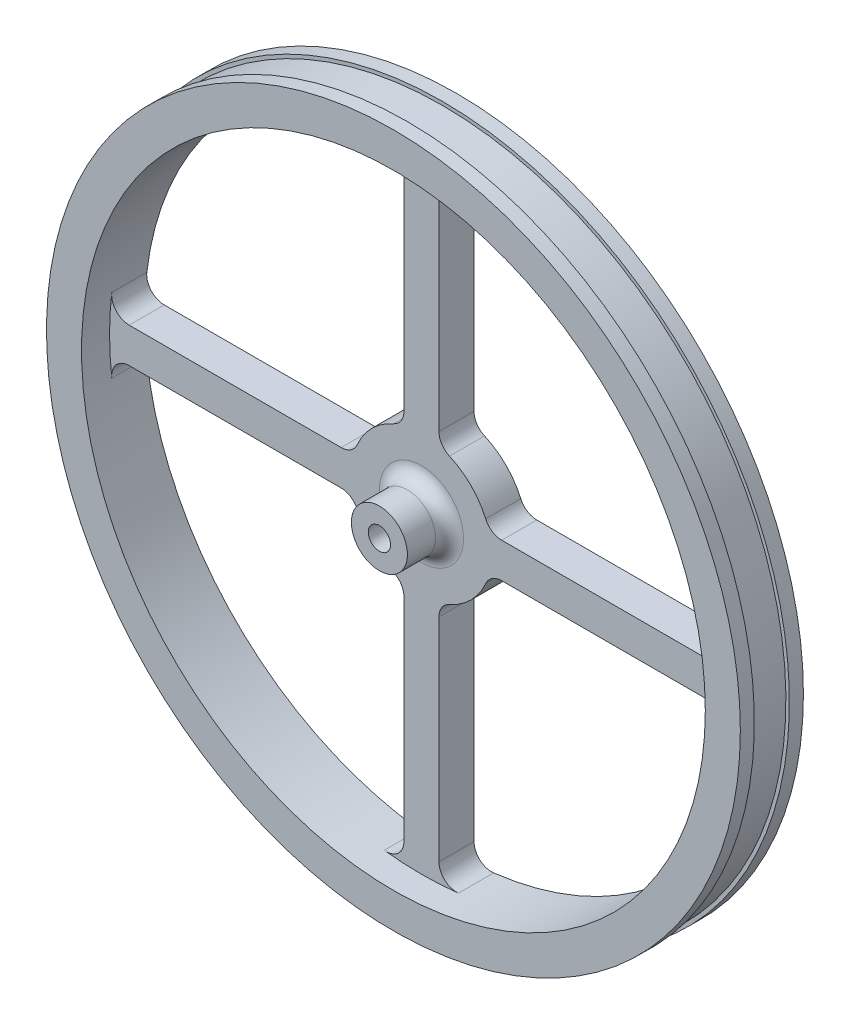
SolidWorks part; units mm, degrees
ref_plane "Front Plane" through (0, 0, 0) normal (0, 0, 1) x (1, 0, 0)
ref_plane "Top Plane" through (0, 0, 0) normal (0, 1, 0) x (1, 0, 0)
ref_plane "Right Plane" through (0, 0, 0) normal (1, 0, 0) x (0, 0, -1)
sketch "Sketch1" plane through (0, 0, 0) normal (0, 0, 1) x (1, 0, 0)
  circle A0 centre (0, 0) radius 49.5
  circle A1 centre (0, 0) radius 1.5875
  dimension "D1" = 99
  dimension "D2" = 3.175
extrude "Boss-Extrude1" add sketch "Sketch1" along normal blind 9
sketch "Sketch2" plane through (0, 0, 9) normal (0, 0, 1) x (1, 0, 0)
  line L8 (0, 7.5) -> (0, 47) construction
  line L9 (7.5, 0) -> (47, 0) construction
  line L10 (2.5, 11.4564) -> (2.5, 41.7013)
  line L11 (11.4564, 2.5) -> (41.7013, 2.5)
  line L12 (9.6825, 2.5) -> (44.4297, 2.5) construction
  line L13 (2.5, 9.6825) -> (2.5, 44.4297) construction
  line L18 (-11.4564, 2.5) -> (-41.7013, 2.5)
  line L19 (-2.5, 11.4564) -> (-2.5, 41.7013)
  line L22 (-7.5, 0) -> (-47, 0) construction
  line L23 (0, 7.5) -> (0, 47) construction
  line L32 (-2.5, -11.4564) -> (-2.5, -41.7013)
  line L33 (-11.4564, -2.5) -> (-41.7013, -2.5)
  line L36 (0, -7.5) -> (0, -47) construction
  line L37 (-7.5, 0) -> (-47, 0) construction
  line L40 (11.4564, -2.5) -> (41.7013, -2.5)
  line L41 (2.5, -11.4564) -> (2.5, -41.7013)
  line L44 (7.5, 0) -> (47, 0) construction
  line L45 (0, -7.5) -> (0, -47) construction
  line L58 (0, 0) -> (0, -14.5334) [skipped]
  line L59 (0, 0) -> (-57.9228, 0) [skipped]
  circle A1 centre (0, 0) radius 49.5 construction
  arc A33 (7.5, 0) -> (0, 7.5) centre (0, 0) ccw construction
  arc A36 (47, 0) -> (0, 47) centre (0, 0) ccw construction
  arc A46 (44.1835, 5.2976) -> (5.2976, 44.1835) centre (0, 0) ccw
  arc A53 (9.1652, 4) -> (4, 9.1652) centre (0, 0) ccw
  arc A54 (44.4297, 2.5) -> (2.5, 44.4297) centre (0, 0) ccw construction
  arc A61 (44.1835, 5.2976) -> (41.7013, 2.5) centre (41.7013, 5) cw
  arc A62 (9.6825, 2.5) -> (2.5, 9.6825) centre (0, 0) ccw construction
  arc A69 (11.4564, 2.5) -> (9.1652, 4) centre (11.4564, 5) cw
  arc A70 (2.5, 11.4564) -> (4, 9.1652) centre (5, 11.4564) ccw
  arc A77 (2.5, 41.7013) -> (5.2976, 44.1835) centre (5, 41.7013) cw
  arc A78 (-5.2976, 44.1835) -> (-44.1835, 5.2976) centre (0, 0) ccw
  arc A85 (-4, 9.1652) -> (-9.1652, 4) centre (0, 0) ccw
  arc A86 (-5.2976, 44.1835) -> (-2.5, 41.7013) centre (-5, 41.7013) cw
  arc A93 (-2.5, 11.4564) -> (-4, 9.1652) centre (-5, 11.4564) cw
  arc A94 (-11.4564, 2.5) -> (-9.1652, 4) centre (-11.4564, 5) ccw
  arc A96 (-41.7013, 2.5) -> (-44.1835, 5.2976) centre (-41.7013, 5) cw
  arc A97 (0, 7.5) -> (-7.5, 0) centre (0, 0) ccw construction
  arc A98 (0, 47) -> (-47, 0) centre (0, 0) ccw construction
  arc A99 (-44.1835, -5.2976) -> (-5.2976, -44.1835) centre (0, 0) ccw
  arc A100 (-9.1652, -4) -> (-4, -9.1652) centre (0, 0) ccw
  arc A101 (-44.1835, -5.2976) -> (-41.7013, -2.5) centre (-41.7013, -5) cw
  arc A102 (-11.4564, -2.5) -> (-9.1652, -4) centre (-11.4564, -5) cw
  arc A103 (-2.5, -11.4564) -> (-4, -9.1652) centre (-5, -11.4564) ccw
  arc A104 (-2.5, -41.7013) -> (-5.2976, -44.1835) centre (-5, -41.7013) cw
  arc A105 (-7.5, 0) -> (0, -7.5) centre (0, 0) ccw construction
  arc A106 (-47, 0) -> (0, -47) centre (0, 0) ccw construction
  arc A107 (5.2976, -44.1835) -> (44.1835, -5.2976) centre (0, 0) ccw
  arc A108 (4, -9.1652) -> (9.1652, -4) centre (0, 0) ccw
  arc A109 (5.2976, -44.1835) -> (2.5, -41.7013) centre (5, -41.7013) cw
  arc A110 (2.5, -11.4564) -> (4, -9.1652) centre (5, -11.4564) cw
  arc A111 (11.4564, -2.5) -> (9.1652, -4) centre (11.4564, -5) ccw
  arc A112 (41.7013, -2.5) -> (44.1835, -5.2976) centre (41.7013, -5) cw
  arc A113 (0, -7.5) -> (7.5, 0) centre (0, 0) ccw construction
  arc A114 (0, -47) -> (47, 0) centre (0, 0) ccw construction
  point P15 (0, 0)
  point P41 (0, 0)
  point P58 (0, 0)
  point P86 (0, 0)
  point P99 (0, 0)
  dimension "D1" = 4
  dimension "D2" = 2.5
  dimension "D4" = 5
  dimension "D3" = 2.5
  dimension "D5" = 10
extrude "Cut-Extrude1" cut sketch "Sketch2" against normal through all
sketch "Sketch3" plane through (0, 0, 9) normal (0, 0, 1) x (1, 0, 0)
  circle A0 centre (0, 0) radius 4
  circle A1 centre (0, 0) radius 44.5
  circle A2 centre (0, 0) radius 49.5 construction
  dimension "D1" = 8
  dimension "D2" = 5
extrude "Cut-Extrude2" cut sketch "Sketch3" against normal blind 4
sketch "Sketch4" plane through (0, 0, 9) normal (0, 0, 1) x (1, 0, 0)
  circle A0 centre (0, 0) radius 4
  circle A1 centre (0, 0) radius 1.5875
  dimension "D1" = 3.175
extrude "Boss-Extrude2" add sketch "Sketch4" along normal blind 2 contours A0
fillet "Fillet1" radius 2 1 edges at (4, 0, 5)
sketch "Sketch5" plane through (0, 0, 0) normal (1, 0, 0) x (0, 0, -1)
  line L0 (0, 49.5) -> (-9, 49.5) construction
  line L1 (-2, 49.5) -> (-7, 49.5)
  line L2 (-2, 49.5) -> (-2, 49)
  line L3 (-2, 49) -> (-7, 49)
  line L4 (-7, 49.5) -> (-7, 49)
  line L5 (0, -49.5) -> (0, 49.5) construction
  line L6 (-9, 49.5) -> (-9, -49.5) construction
  line L7 (0, 0) -> (-11, 0) construction
  line L8 (-11, 4) -> (-11, -4) construction
  dimension "D1" = 2
  dimension "D2" = 2
  dimension "D3" = 0.5
revolve "Cut-Revolve1" cut sketch "Sketch5" angle 360 about L7
